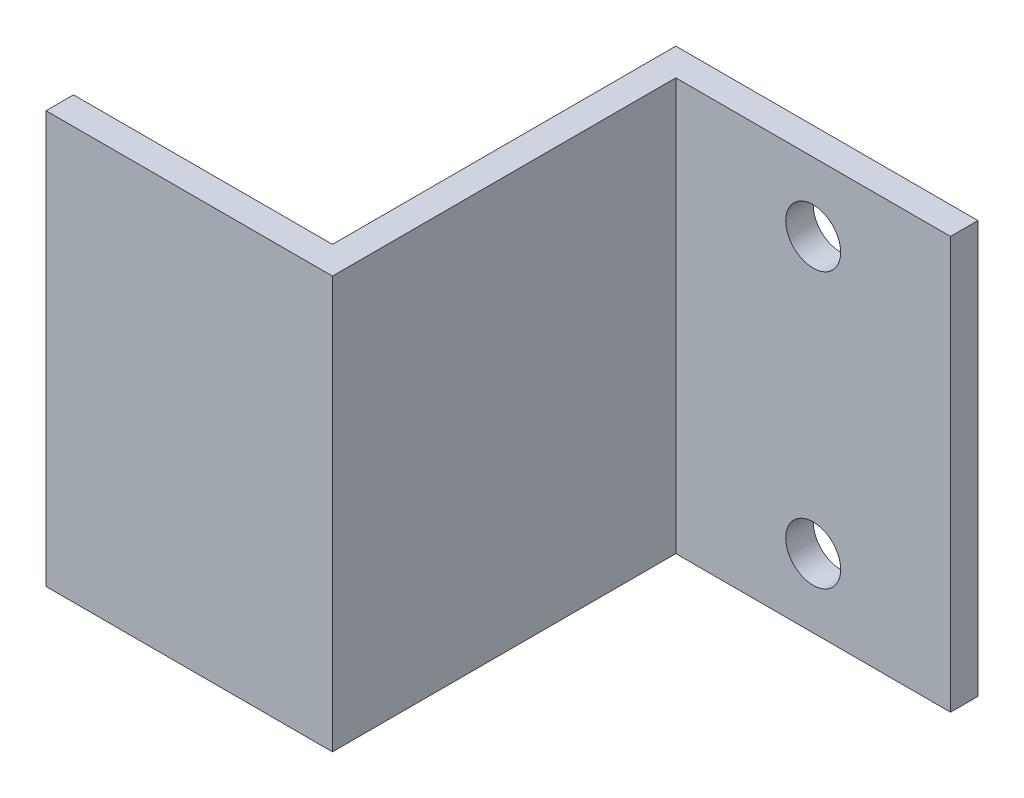
SolidWorks part; units mm, degrees
ref_plane "Спереди" through (0, 0, 0) normal (0, 0, 1) x (1, 0, 0)
ref_plane "Сверху" through (0, 0, 0) normal (0, 1, 0) x (1, 0, 0)
ref_plane "Справа" through (0, 0, 0) normal (1, 0, 0) x (0, 0, -1)
sketch "Эскиз1" plane through (0, 0, 0) normal (0, 1, 0) x (1, 0, 0)
  line L0 (0, 0) -> (-20.8563, 0)
  line L1 (-20.8563, 0) -> (-20.8563, 2)
  line L2 (-20.8563, 2) -> (-2, 2)
  line L3 (-2, 2) -> (-2, 27)
  line L4 (-2, 27) -> (20, 27)
  line L5 (20, 27) -> (20, 25)
  line L6 (20, 25) -> (0, 25)
  line L7 (0, 25) -> (0, 0)
extrude "Бобышка-Вытянуть1" add sketch "Эскиз1" along normal blind 30
sketch "Эскиз2" plane through (0, 0, -27) normal (0, 0, -1) x (-1, 0, 0)
  circle A0 centre (-10, 25) radius 2
  circle A1 centre (-10, 5) radius 2
  dimension "D1" = 2
extrude "Вырез-Вытянуть1" cut sketch "Эскиз2" against normal through all
